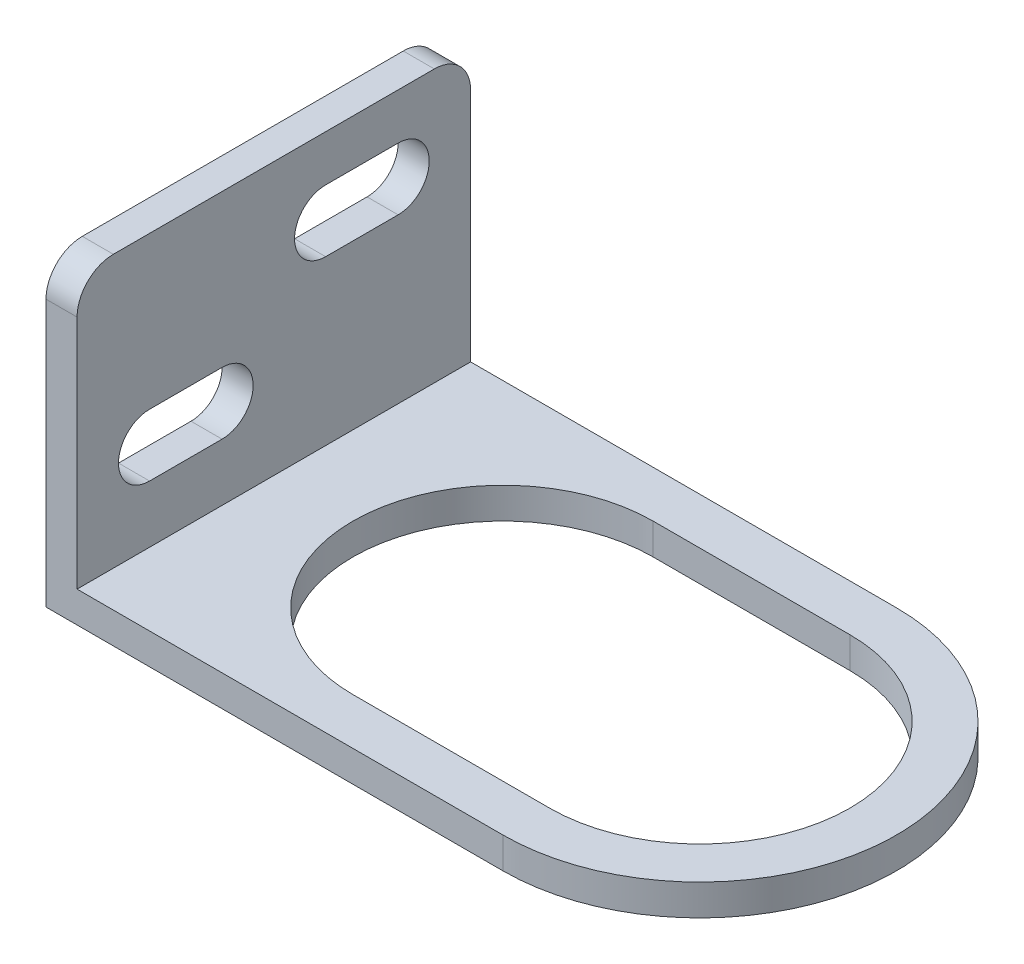
SolidWorks part; units mm, degrees
ref_plane "Front Plane" through (0, 0, 0) normal (0, 0, 1) x (1, 0, 0)
ref_plane "Top Plane" through (0, 0, 0) normal (0, 1, 0) x (1, 0, 0)
ref_plane "Right Plane" through (0, 0, 0) normal (1, 0, 0) x (0, 0, -1)
sketch "Sketch2" plane through (0, 0, 0) normal (0, 0, 1) x (1, 0, 0)
  line L0 (0, 32) -> (0, 0)
  line L1 (0, 0) -> (63, 0)
  dimension "D1" = 63
  dimension "D2" = 32
extrude "Extrude-Thin1" add sketch "Sketch2" along normal mid plane 38 thin thin type mid plane wall 3
sketch "Sketch3" plane through (1.5, 0, 0) normal (1, 0, 0) x (0, 0, -1)
  line L0 (5, 20.2986) -> (12, 20.2986) construction
  line L1 (5, 23.2986) -> (12, 23.2986)
  line L2 (5, 17.2986) -> (12, 17.2986)
  line L3 (-12, 10.0399) -> (-5, 10.0399) construction
  line L4 (-12, 13.0399) -> (-5, 13.0399)
  line L5 (-12, 7.0399) -> (-5, 7.0399)
  line L6 (0, 10.0399) -> (0, 27.7496) construction
  line L7 (-5, 10.0399) -> (0, 10.0399) construction
  line L8 (5, 20.2986) -> (0, 20.2986) construction
  line L9 (-92.2123, 66.1017) -> (-41.9505, 66.1017) construction
  line L10 (-19, 32) -> (-19, 1.5) construction
  line L11 (19, 32) -> (19, 1.5) construction
  line L14 (-15.4965, 27.7496) -> (15.4965, 27.7496)
  line L15 (-19, 32) -> (19, 32) construction
  line L16 (-19, 32) -> (19, 32)
  line L17 (-19, 32) -> (-19, 24.2461)
  line L18 (19, 32) -> (19, 24.2461)
  arc A0 (5, 23.2986) -> (5, 17.2986) centre (5, 20.2986) ccw
  arc A1 (12, 17.2986) -> (12, 23.2986) centre (12, 20.2986) ccw
  arc A2 (-12, 13.0399) -> (-12, 7.0399) centre (-12, 10.0399) ccw
  arc A3 (-5, 7.0399) -> (-5, 13.0399) centre (-5, 10.0399) ccw
  arc A4 (-19, 24.2461) -> (-15.4965, 27.7496) centre (-15.4965, 24.2461) cw
  arc A5 (19, 24.2461) -> (15.4965, 27.7496) centre (15.4965, 24.2461) ccw
  point P2 (8.5, 20.2986)
  point P7 (-8.5, 10.0399)
  dimension "D1" = 7
  dimension "D2" = 24
  dimension "D3" = 6
extrude "Cut-Extrude1" cut sketch "Sketch3" against normal through all
sketch "Sketch4" plane through (0, 1.5, 0) normal (0, 1, 0) x (1, 0, 0)
  line L0 (83.1348, -6.136) -> (83.1348, 92.5307) construction
  line L1 (42.6257, 0) -> (23.6257, 0) construction
  line L2 (42.6257, -14.5) -> (23.6257, -14.5)
  line L3 (42.6257, 14.5) -> (23.6257, 14.5)
  line L4 (1.5, 19) -> (63, 19) construction
  line L5 (1.5, -19) -> (63, -19) construction
  line L6 (42.6257, 19) -> (63, 19)
  line L7 (42.6257, -19) -> (63, -19)
  line L8 (63, -19) -> (63, 19) construction
  line L9 (63, -19) -> (63, 19)
  arc A0 (42.6257, -14.5) -> (42.6257, 14.5) centre (42.6257, 0) ccw
  arc A1 (23.6257, 14.5) -> (23.6257, -14.5) centre (23.6257, 0) ccw
  arc A2 (42.6257, 19) -> (42.6257, -19) centre (42.6257, 0) cw
  point P5 (33.1257, 0)
  point P17 (57.1257, 0)
  point P18 (61.6257, 0)
  dimension "D3" = 4.5
  dimension "D1" = 19
  dimension "D2" = 29
extrude "Cut-Extrude2" cut sketch "Sketch4" against normal blind 10
